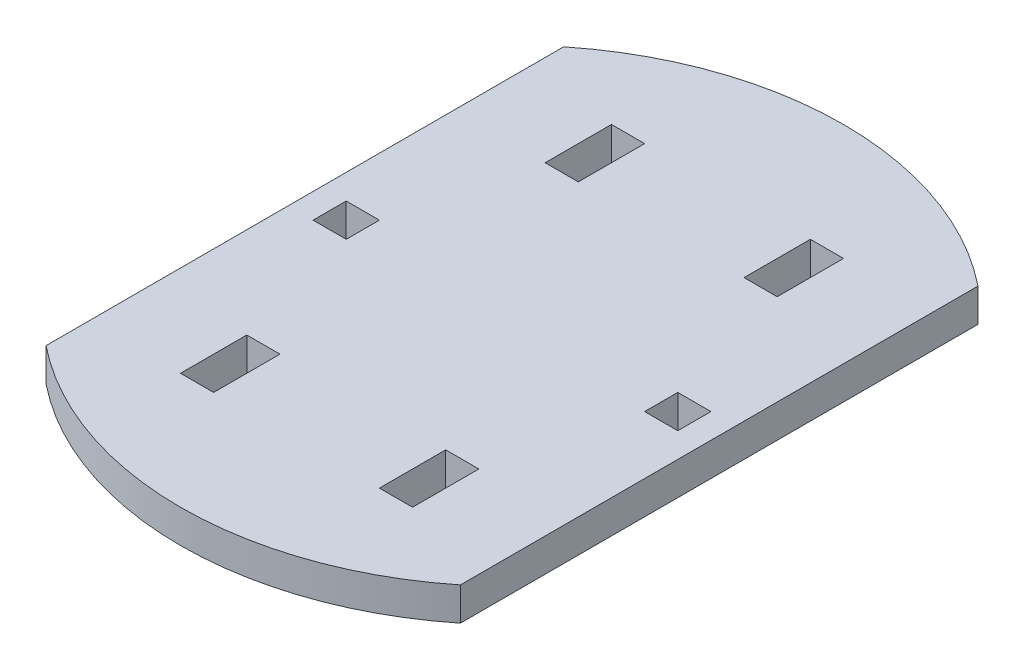
SolidWorks part; units mm, degrees
ref_plane "Front Plane" through (0, 0, 0) normal (0, 0, 1) x (1, 0, 0)
ref_plane "Top Plane" through (0, 0, 0) normal (0, 1, 0) x (1, 0, 0)
ref_plane "Right Plane" through (0, 0, 0) normal (1, 0, 0) x (0, 0, -1)
sketch "Sketch1" plane through (0, 0, 0) normal (0, 1, 0) x (1, 0, 0)
  line L0 (-25, 31.225) -> (-25, -31.225)
  line L1 (0, 0) -> (0, 40) construction
  line L2 (25, 31.225) -> (25, -31.225)
  line L3 (0, 0) -> (20, 0) construction
  line L4 (-18, -2) -> (-22, -2)
  line L5 (18, 2) -> (22, 2)
  line L6 (18, 2) -> (18, -2)
  line L7 (18, -2) -> (22, -2)
  line L8 (22, 2) -> (22, -2)
  line L9 (18, 2) -> (22, -2) construction
  line L10 (18, -2) -> (22, 2) construction
  line L11 (-22, 2) -> (-22, -2)
  line L12 (-18, 2) -> (-22, 2)
  line L13 (-18, 2) -> (-18, -2)
  line L19 (14, 18) -> (10, 18)
  line L20 (-14, 26) -> (-10, 26)
  line L21 (-14, 26) -> (-14, 18)
  line L22 (-14, 18) -> (-10, 18)
  line L23 (-10, 26) -> (-10, 18)
  line L24 (10, 26) -> (10, 18)
  line L25 (14, 26) -> (10, 26)
  line L26 (14, 26) -> (14, 18)
  line L27 (14, -26) -> (14, -18)
  line L28 (14, -26) -> (10, -26)
  line L29 (10, -26) -> (10, -18)
  line L30 (14, -18) -> (10, -18)
  line L31 (-14, -18) -> (-10, -18)
  line L32 (-10, -26) -> (-10, -18)
  line L33 (-14, -26) -> (-10, -26)
  line L34 (-14, -26) -> (-14, -18)
  circle A0 centre (0, 0) radius 40
  dimension "D1" = 80
  dimension "D2" = 8
  dimension "D3" = 4
  dimension "D4" = 20
  dimension "D5" = 4
  dimension "D6" = 15
  dimension "D7" = 18
extrude "Boss-Extrude1" add sketch "Sketch1" along normal blind 4
